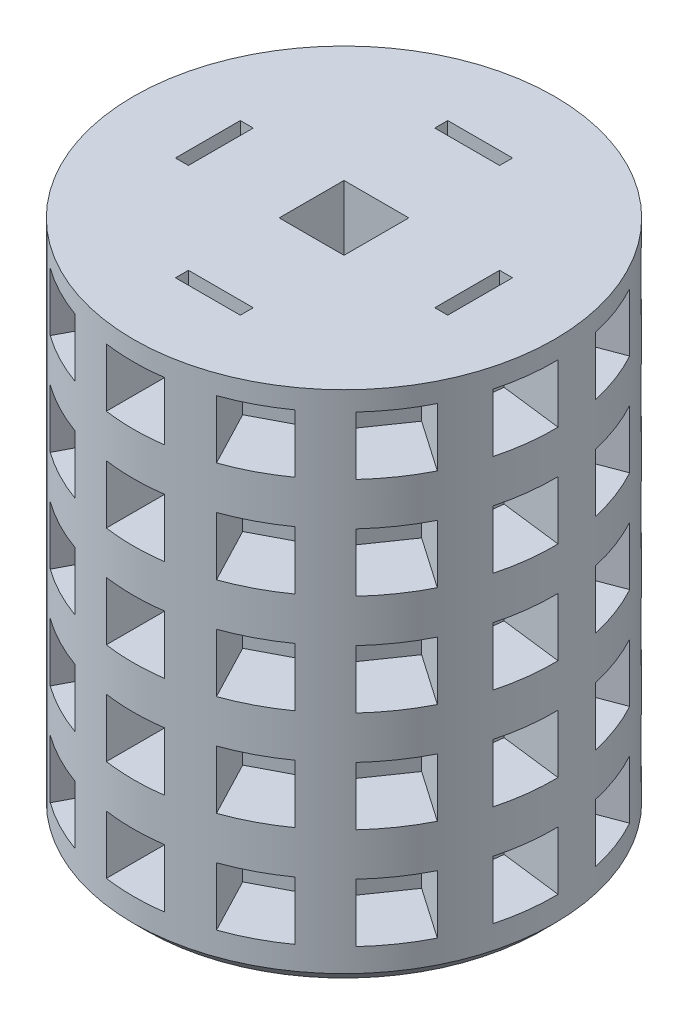
SolidWorks part; units mm, degrees
ref_plane "Front Plane" through (0, 0, 0) normal (0, 0, 1) x (1, 0, 0)
ref_plane "Top Plane" through (0, 0, 0) normal (0, 1, 0) x (1, 0, 0)
ref_plane "Right Plane" through (0, 0, 0) normal (1, 0, 0) x (0, 0, -1)
sketch "Sketch1" plane through (0, 0, 0) normal (0, 1, 0) x (1, 0, 0)
  circle A0 centre (0, 0) radius 41.2369
  dimension "D1" = 82.4738
extrude "Boss-Extrude1" add sketch "Sketch1" along normal blind 203.2 contours A0
sketch "Sketch2" plane through (0, 0, 0) normal (0, -1, 0) x (-1, 0, 0)
  line L3 (0, -6.35) -> (6.35, -6.35)
  line L5 (0, 6.35) -> (6.35, 6.35)
  line L6 (6.35, -6.35) -> (6.35, 6.35)
  line L7 (0, -6.35) -> (-6.35, -6.35)
  line L9 (0, 6.35) -> (-6.35, 6.35)
  line L10 (-6.35, -6.35) -> (-6.35, 6.35)
extrude "Cut-Extrude1" cut sketch "Sketch2" against normal through all contours L10 L9 L5 L6 L3 L7
ref_plane "Plane2" through (0, 0, 60.96) normal (0, 0, 1) x (1, 0, 0)
chamfer "Chamfer1" distance 2.54 angle 45 1 edges at (0, 203.2, 41.2369)
chamfer "Chamfer2" distance 2.54 angle 45 1 edges at (0, 0, 41.2369)
ref_plane "Plane3" through (0, 0, 48.26) normal (0, 0, 1) x (1, 0, 0)
ref_plane "Plane4" through (0, 0, 41.402) normal (0, 0, 1) x (1, 0, 0)
sketch "Sketch3" plane through (0, 0, 41.402) normal (0, 0, 1) x (1, 0, 0)
  line L0 (-41.2369, 200.66) -> (41.2369, 200.66) construction
  line L1 (0, 200.66) -> (-9.525, 200.66)
  line L2 (-9.525, 200.66) -> (9.525, 181.61)
  line L3 (-3.81, 181.61) -> (-9.525, 181.61)
  line L4 (-9.525, 200.66) -> (-9.525, 181.61)
  line L5 (-9.525, 181.61) -> (9.525, 200.66)
  line L6 (0, 200.66) -> (9.525, 200.66)
  line L8 (-3.81, 181.61) -> (9.525, 181.61)
  line L9 (9.525, 200.66) -> (9.525, 181.61)
sketch "Sketch6" plane through (0, 0, 41.402) normal (0, 0, 1) x (1, 0, 0)
  line L0 (-9.525, 181.61) -> (9.525, 200.66) construction
  line L3 (0, 196.85) -> (5.715, 196.85)
  line L4 (5.715, 191.135) -> (5.715, 196.85)
  line L5 (-9.525, 200.66) -> (9.525, 181.61) construction
  line L8 (0, 196.85) -> (-5.715, 196.85)
  line L9 (-5.715, 191.135) -> (-5.715, 196.85)
  line L12 (-5.715, 191.135) -> (-5.715, 185.42)
  line L13 (-5.715, 185.42) -> (5.715, 185.42)
  line L14 (5.715, 191.135) -> (5.715, 185.42)
extrude "Cut-Extrude3" cut sketch "Sketch6" against normal blind 12.7 contours L3 L4 L14 L13 L12 L9 L8
pattern_linear "LPattern1" count 10 spacing 19.812 along (0, -1, 0) of "Cut-Extrude3"
pattern_circular "CirPattern1" count 13 every 27.7 about axis through (0, 0, 0) along (0, 1, 0) of "LPattern1", "Cut-Extrude3"
sketch "Sketch7" plane through (0, 203.2, 0) normal (0, 1, 0) x (1, 0, 0)
  circle A0 centre (0, 0) radius 41.2369
extrude "Cut-Extrude4" cut sketch "Sketch7" against normal blind 101.6 contours A0
sketch "Sketch8" plane through (0, 101.6, 0) normal (0, 1, 0) x (1, 0, 0)
  line L3 (6.35, 6.35) -> (-6.35, 6.35) construction
  line L4 (-6.35, 26.67) -> (6.35, 26.67)
  line L5 (-6.35, 26.67) -> (-6.35, 24.13)
  line L6 (-6.35, 24.13) -> (6.35, 24.13)
  line L7 (6.35, 26.67) -> (6.35, 24.13)
  line L8 (-6.35, 26.67) -> (6.35, 24.13) construction
  line L9 (-6.35, 24.13) -> (6.35, 26.67) construction
  line L10 (24.13, -6.35) -> (26.67, -6.35)
  line L11 (24.13, -6.35) -> (24.13, 6.35)
  line L12 (24.13, 6.35) -> (26.67, 6.35)
  line L13 (26.67, -6.35) -> (26.67, 6.35)
  line L14 (24.13, -6.35) -> (26.67, 6.35) construction
  line L15 (24.13, 6.35) -> (26.67, -6.35) construction
  line L16 (-6.35, -24.13) -> (6.35, -24.13)
  line L17 (-6.35, -24.13) -> (-6.35, -26.67)
  line L18 (-6.35, -26.67) -> (6.35, -26.67)
  line L19 (6.35, -24.13) -> (6.35, -26.67)
  line L20 (-6.35, -24.13) -> (6.35, -26.67) construction
  line L21 (-6.35, -26.67) -> (6.35, -24.13) construction
  line L22 (-26.67, -6.35) -> (-24.13, -6.35)
  line L23 (-26.67, -6.35) -> (-26.67, 6.35)
  line L24 (-26.67, 6.35) -> (-24.13, 6.35)
  line L25 (-24.13, -6.35) -> (-24.13, 6.35)
  line L26 (-26.67, -6.35) -> (-24.13, 6.35) construction
  line L27 (-26.67, 6.35) -> (-24.13, -6.35) construction
  line L28 (6.35, -6.35) -> (6.35, 6.35) construction
  line L29 (6.35, -6.35) -> (-6.35, -6.35) construction
  line L30 (-6.35, -6.35) -> (-6.35, 6.35) construction
  point P4 (0, 25.4)
  point P11 (25.4, 0)
  point P16 (0, -25.4)
  point P21 (-25.4, 0)
  dimension "D1" = 19.05
  dimension "D2" = 19.05
  dimension "D3" = 19.05
  dimension "D4" = 19.05
  dimension "D5" = 2.54
  dimension "D6" = 12.7
  dimension "D7" = 2.54
  dimension "D8" = 12.7
  dimension "D9" = 12.7
  dimension "D10" = 2.54
  dimension "D11" = 2.54
  dimension "D12" = 12.7
sketch "Sketch9" plane through (0, 0, 0) normal (0, -1, 0) x (-1, 0, 0)
  line L1 (-6.35, -6.35) -> (6.35, -6.35)
  line L2 (-6.35, -6.35) -> (-6.35, 6.35)
  line L3 (-6.35, 6.35) -> (6.35, 6.35)
  line L4 (6.35, -6.35) -> (6.35, 6.35)
  circle A0 centre (0, 0) radius 20.32
extrude "Boss-Extrude4" add sketch "Sketch9" along normal blind 9.906
extrude "Cut-Extrude6" cut sketch "Sketch8" against normal blind 12.7
